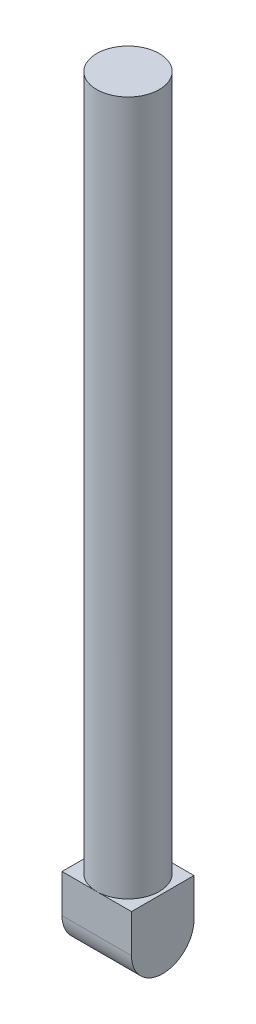
SolidWorks part; units mm, degrees
ref_plane "Front" through (0, 0, 0) normal (0, 0, 1) x (1, 0, 0)
ref_plane "Top" through (0, 0, 0) normal (0, 1, 0) x (1, 0, 0)
ref_plane "Right" through (0, 0, 0) normal (1, 0, 0) x (0, 0, -1)
sketch "草图1" plane through (0, 0, 0) normal (0, 1, 0) x (1, 0, 0)
  line L1 (-10, 9) -> (10, 9)
  line L2 (-10, 9) -> (-10, -9)
  line L3 (-10, -9) -> (10, -9)
  line L4 (10, 9) -> (10, -9)
  dimension "D1" = 20
  dimension "D2" = 18
  dimension "D3" = 10
  dimension "D4" = 9
extrude "凸台-拉伸1" add sketch "草图1" along normal blind 20
sketch "草图2" plane through (0, 20, 0) normal (0, 1, 0) x (1, 0, 0)
  circle A0 centre (0, 0) radius 9
extrude "凸台-拉伸2" add sketch "草图2" along normal blind 200
sketch "草图3" plane through (-10, 0, 0) normal (-1, 0, 0) x (0, 0, 1)
  line L2 (-9, 9) -> (-9, -3.6696)
  line L3 (-9, -3.6696) -> (9, -3.6696)
  line L4 (9, 9) -> (9, -3.6696)
  arc A0 (-9, 9) -> (9, 9) centre (0, 9) ccw
extrude "切除-拉伸1" cut sketch "草图3" against normal blind 100
